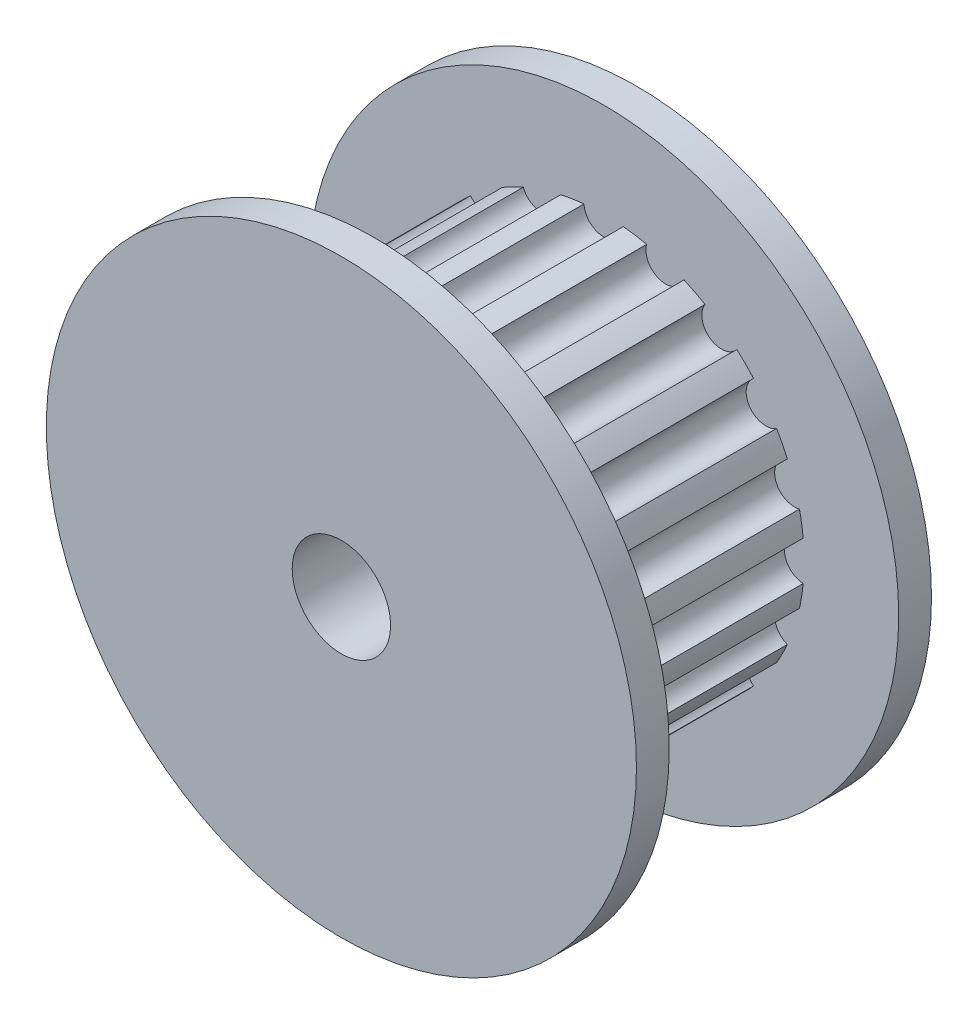
SolidWorks part; units mm, degrees
material "6061 合金"
ref_plane "前基準面" through (0, 0, 0) normal (0, 0, 1) x (1, 0, 0)
ref_plane "上基準面" through (0, 0, 0) normal (0, 1, 0) x (1, 0, 0)
ref_plane "右基準面" through (0, 0, 0) normal (1, 0, 0) x (0, 0, -1)
sketch "草圖1" plane through (0, 0, 0) normal (0, 0, 1) x (1, 0, 0)
  circle A0 centre (0, 0) radius 9
  dimension "D1" = 18
extrude "填料-伸長1" add sketch "草圖1" along normal mid plane 1
sketch "草圖2" plane through (0, 0, 0.5) normal (0, 0, 1) x (1, 0, 0)
  circle A0 centre (0, 0) radius 6.115
  dimension "D1" = 12.23
extrude "填料-伸長2" add sketch "草圖2" along normal blind 7
sketch "草圖7" plane through (0, 0, 7.5) normal (0, 0, 1) x (1, 0, 0)
  line L0 (0, 0) -> (0, 6.115) construction
  arc A0 (-0.5993, 6.0856) -> (0.5993, 6.0856) centre (0, 6.115) ccw
  circle A1 centre (0, 0) radius 6.115 construction
  circle A2 centre (0, 0) radius 6.115 construction
  arc A3 (-0.5993, 6.0856) -> (0.5993, 6.0856) centre (0, 0) cw
  point P10 (0, 5.515)
  dimension "D1" = 0.6
extrude "除料-伸長3" cut sketch "草圖7" against normal up to surface (7 mm away) up to face at (6.115, 0, 0.5)
sketch "草圖3" plane through (0, 0, 7.5) normal (0, 0, 1) x (1, 0, 0)
  circle A0 centre (0, 0) radius 9
  circle A1 centre (0, 0) radius 9 construction
extrude "填料-伸長3" add sketch "草圖3" along normal blind 1
sketch "草圖6" plane through (0, 0, -0.5) normal (0, 0, -1) x (-1, 0, 0)
  circle A0 centre (0, 0) radius 1.5
  dimension "D1" = 3
extrude "除料-伸長2" cut sketch "草圖6" against normal through all
pattern_circular "環狀複製排列2" count 20 over 360 about axis through (0, 0, 0) along (0, 0, 1) of "除料-伸長3"
